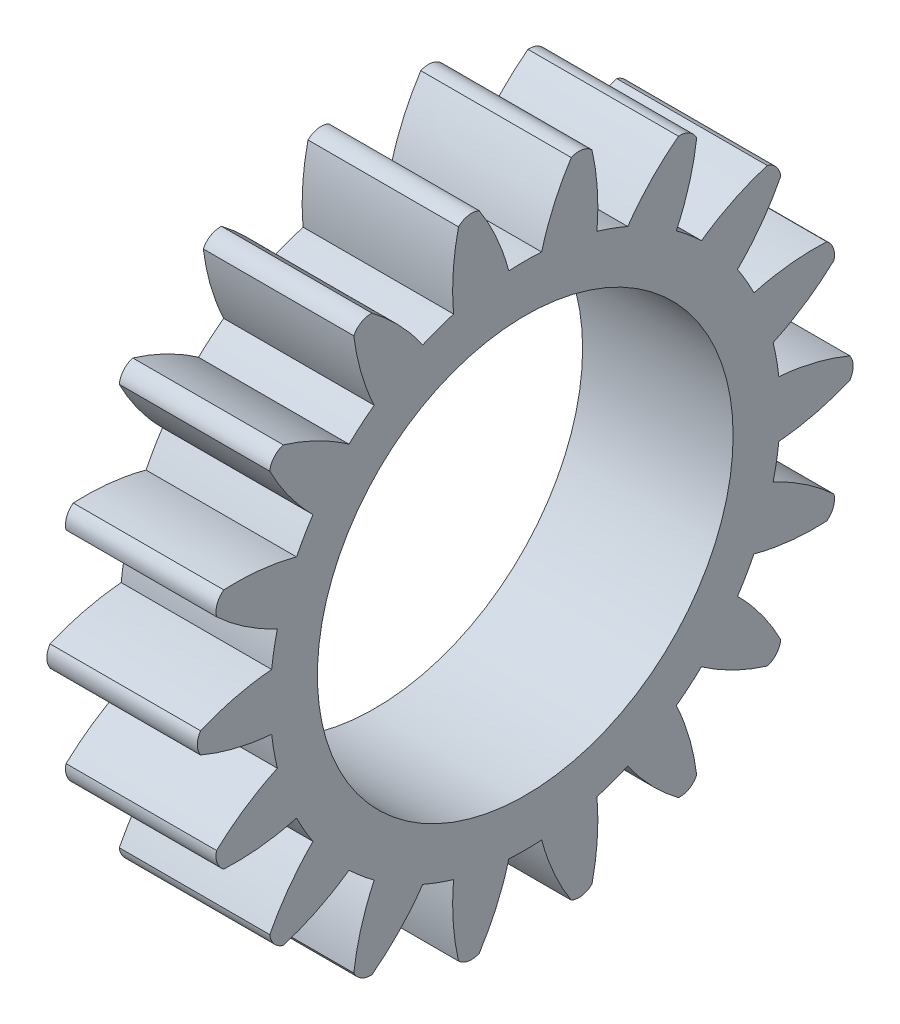
SolidWorks part; units mm, degrees
material "PLA personnalisé"
ref_plane "Plane1" through (0, 0, 0) normal (0, 0, 1) x (1, 0, 0)
ref_plane "Plane2" through (0, 0, 0) normal (0, 1, 0) x (1, 0, 0)
ref_plane "Plane3" through (0, 0, 0) normal (1, 0, 0) x (0, 0, -1)
other "Configuration Table"
sketch "HoldingSke" plane through (0, 0, 0) normal (0, 1, 0) x (1, 0, 0)
  line L0 (0, 0) -> (0.5435, -0.1766)
  line L1 (-15, 0) -> (100, 0) construction
  line L2 (0, 0) -> (-2.1039, 2.3779)
  line L3 (0, 0) -> (-11.863, 4.5341)
  line L4 (0, 0) -> (8.2133, 2.6687)
  line L5 (0, 0) -> (-46.8476, -17.4728)
  line L6 (0, 0) -> (-6.6317, -4.4744)
  line L7 (-2.1039, 2.3779) -> (8.6586, 51.2059)
  line L8 (-76.2, 54.61) -> (-74.8, 54.61)
  line L9 (-71.009, 38.7566) -> (-53.1078, 45.2721)
  line L10 (-76.2, 71.12) -> (104.1128, 71.12)
  line L11 (0, 0) -> (-8, 0)
  line L12 (-76.2, 101.6) -> (-76.147, 101.6)
  line L13 (24.9733, 27.94) -> (52.9518, 28.4284)
  line L14 (24.9733, 27.94) -> (24.9743, 27.94)
  line L15 (24.9733, 27.94) -> (100.4006, 29.5858)
  line L16 (-63.627, -1.75) -> (-12.827, -1.75)
  circle A0 centre (0, 0) radius 4
  circle A1 centre (0, 0) radius 13.5615
  circle A2 centre (0, 0) radius 37.5
  circle A3 centre (0, 0) radius 4
  dimension "MHD" = 27.123
  dimension "Hub_dia" = 75
  dimension "Bore" = 8
  dimension "MBD" = 8
  dimension "Num_teeth" = 18
  dimension "Pitch" = 0.5714
  dimension "Overall_len" = 50
  dimension "Show_teeth" = 18
  dimension "Thickness" = 8
  dimension "OAL" = 50.0001
  dimension "T_dim" = 1.4
  dimension "Ap" = 20
  dimension "H" = 19.05
  dimension "Pitch_radius" = 180.3128
  dimension "Width" = 8
  dimension "Backlash" = 0.053
  dimension "Addendum_fac" = 1
  dimension "Dedendum_fac" = 1.25
  dimension "Clearance_fac" = 0.25
  dimension "Dedendum_add" = 0.001
  dimension "Module" = 1.75
sketch "BasProSke" plane through (0, 0, 0) normal (0, 1, 0) x (1, 0, 0)
  line L0 (-10, 0) -> (60, 0) construction
  line L1 (0, 0) -> (0, 17.5)
  line L2 (0, 0) -> (8, 0)
  line L3 (8, 0) -> (8, 17.5)
  line L4 (8, 17.5) -> (0, 17.5)
  dimension "Thickness" = 8
  dimension "Diameter" = 35
revolve "Base-Revolve" add sketch "BasProSke" angle 360 about L0
sketch "TooCutSke" plane through (0, 0, 0) normal (1, 0, 0) x (0, 0, -1)
  line L1 (0, 0) -> (0, 107) construction
  line L2 (0, 0) -> (-1.4654, 15.6817) construction
  line L3 (0, 0) -> (-5.4518, 30.9188) construction
  line L4 (-1.4654, 15.6817) -> (-2.7259, 15.4594) construction
  arc A0 (0.8733, 13.5334) -> (-0.8733, 13.5334) centre (0, 0) ccw
  arc A1 (2.6093, 17.3301) -> (-2.6093, 17.3301) centre (0, 0) ccw
  circle A2 centre (0, 0) radius 15.75 construction
  circle A3 centre (0, 0) radius 14.8002 construction
  arc A4 (-0.8733, 13.5334) -> (-2.6093, 17.3301) centre (-7.1472, 12.96) ccw
  arc A5 (2.6093, 17.3301) -> (0.8733, 13.5334) centre (7.1472, 12.96) ccw
  dimension "Root_dia" = 27.123
  dimension "Overcut_dia" = 35.0508
  dimension "Pitch_dia" = 31.5
  dimension "Base_dia" = 29.6003
  dimension "Flank_rad" = 6.3
  dimension "Half_ang" = 10
  dimension "Half_CT" = 1.28
extrude "ToothCut" cut sketch "TooCutSke" along normal through all
fillet "Breaks" [suppressed] radius 0.035
fillet "RootFillets" [suppressed] radius 0.4385
pattern_circular "TeethCuts" count 18 every 20 about axis through (-10, 0, 0) along (1, 0, 0) of "ToothCut", "RootFillets", "Breaks"
sketch "HubNeaOneSke" plane through (0, 0, 0) normal (-1, 0, 0) x (0, 0, 1)
  circle A0 centre (0, 0) radius 13.5615
  dimension "Diameter" = 27.123
extrude "HubNearOne" [suppressed] add sketch "HubNeaOneSke" along normal blind 42.0001
sketch "HubNeaBotSke" plane through (0, 0, 0) normal (-1, 0, 0) x (0, 0, 1)
  circle A0 centre (0, 0) radius 13.5615
  dimension "Diameter" = 27.123
extrude "HubNearBoth" [suppressed] add sketch "HubNeaBotSke" along normal blind 21
ref_plane "FarPln" through (8, 0, 0) normal (1, 0, 0) x (0, 0, -1)
sketch "HubFarSke" plane through (8, 0, 0) normal (1, 0, 0) x (0, 0, -1)
  circle A0 centre (0, 0) radius 13.5615
  dimension "Diameter" = 27.123
extrude "HubFar" [suppressed] add sketch "HubFarSke" along normal blind 21
sketch "BorSke" plane through (0, 0, 0) normal (1, 0, 0) x (0, 0, -1)
  circle A0 centre (0, 0) radius 4
  dimension "Diameter" = 8
extrude "Bore" cut sketch "BorSke" along normal mid plane 100.0001
sketch "KeySke" plane through (0, 0, 0) normal (1, 0, 0) x (0, 0, -1)
  line L0 (-1.5, 0) -> (-1.5, 5.4)
  line L1 (-1.5, 5.4) -> (1.5, 5.4)
  line L2 (1.5, 5.4) -> (1.5, 0)
  line L3 (0, 0) -> (0, 34) construction
  line L4 (-1.5, 0) -> (1.5, 0)
  dimension "Offset" = 5.4
  dimension "Width" = 3
extrude "Keyway" [suppressed] cut sketch "KeySke" along normal mid plane 100.0001
pattern_circular "Keyway2" [suppressed] count 2 every 90 about axis through (-10, 0, 0) along (1, 0, 0)
sketch "Esquisse1" plane through (8, 0, 0) normal (1, 0, 0) x (0, 0, -1)
  circle A0 centre (0, 0) radius 11.05
  dimension "D1" = 22.1
extrude "Enlèv. mat.-Extru.1" cut sketch "Esquisse1" against normal blind 10
sketch "Esquisse3" plane through (8, 0, 0) normal (1, 0, 0) x (0, 0, -1)
  line L0 (0, 0) -> (17.5, 0) construction
  line L1 (17.494, 0.457) -> (15.5741, 1.3132) construction
  line L2 (15.5741, 1.3132) -> (13.4794, 1.49) construction
  line L3 (13.4794, 1.49) -> (13.914, 2.1775)
  line L4 (13.914, 2.1775) -> (17.9524, 1.0519)
  line L5 (17.9524, 1.0519) -> (17.494, 0.457)
  line L6 (17.9524, 1.0519) -> (17.6593, 0)
  line L7 (17.6593, 0) -> (17.5, 0)
  line L8 (17.5, 0) -> (16.43, 0)
  arc A0 (17.494, -0.457) -> (17.494, 0.457) centre (0, 0) ccw construction
  circle A2 centre (16.43, 0) radius 1
  spline S0 degree 2 poles (17.494, 0.457) (15.5741, 1.3132) (13.4794, 1.49) knots 0 0 0 1 1 1
  dimension "D1" = 2
  dimension "D2" = 1.07
extrude "Enlèv. mat.-Extru.2" cut sketch "Esquisse3" against normal blind 10 contours S0 L5 L4 L3 A2 | L5 S0 A2 L7 L6 | S0 A2
mirror "Symétrie1" about plane through (0, 0, 0) normal (0, 1, 0) of "Enlèv. mat.-Extru.2"
pattern_circular "Répétition circulaire1" count 18 over 360 about axis through (-2, 0, 0) along (1, 0, 0) of "Enlèv. mat.-Extru.2", "Symétrie1"
equation "' \"Module@HoldingSke\" = 6.35"
equation "' \"Num_teeth@HoldingSke\" = 12"
equation "' \"Ap@HoldingSke\" =  20"
equation "' \"Ap@HoldingSke\" = 20"
equation "' \"Width@HoldingSke\" = 0.5 * 25.4"
equation "' \"Hub_dia@HoldingSke\"= 1 * 25.4"
equation "' \"Hub_dia@HoldingSke\" = 1 * 25.4"
equation "' \"Overall_len@HoldingSke\" = 1.0 * 25.4"
equation "' \"Bore@HoldingSke\" = 0.75 * 25.4"
equation "' \"T_dim@HoldingSke\" = 0.1 * 25.4"
equation "' \"Width@KeySke\" = 0.25 * 25.4"
equation "' \"Show_teeth@HoldingSke\" = 13"
equation "' \"Backlash@HoldingSke\" = 0.009 * 25.4"
equation "' \"Addendum_fac@HoldingSke\" = 1.0"
equation "' \"Dedendum_fac@HoldingSke\" = 1.25"
equation "' \"Dedendum_add@HoldingSke\" = 0.00005 * 25.4"
equation "' \"Clearance_fac@HoldingSke\" = 0.25"
equation "\"Pitch@HoldingSke\" = 1 / \"Module@HoldingSke\""
equation "\"Overcut_dia@TooCutSke\" = (\"Num_teeth@HoldingSke\" + 2 * \"Addendum_fac@HoldingSke\") / \"Pitch@HoldingSke\" + 0.002 * 25.4"
equation "\"Pitch_dia@TooCutSke\" = \"Num_teeth@HoldingSke\" / \"Pitch@HoldingSke\""
equation "\"Base_dia@TooCutSke\" = \"Num_teeth@HoldingSke\" / \"Pitch@HoldingSke\" * cos((\"Ap@HoldingSke\"  * 3.14159265 / 180))"
equation "\"Root_dia@TooCutSke\" = (\"Num_teeth@HoldingSke\" + 2) / \"Pitch@HoldingSke\" - 2 * (\"Addendum_fac@HoldingSke\" + \"Dedendum_fac@HoldingSke\") / \"Pitch@HoldingSke\" - \"Dedendum_add@HoldingSke\" * 2"
equation "\"Half_ang@TooCutSke\" = 180 / \"Num_teeth@HoldingSke\""
equation "\"Half_CT@TooCutSke\" = \"Num_teeth@HoldingSke\" / \"Pitch@HoldingSke\" * sin((3.14159265 / 2 / \"Num_teeth@HoldingSke\")) / 2 - 7 * \"Backlash@HoldingSke\" / 4"
equation "\"Flank_rad@TooCutSke\" = \"Num_teeth@HoldingSke\" / \"Pitch@HoldingSke\" / 5"
equation "\"Radius@RootFillets\" = \"Clearance_fac@HoldingSke\" / \"Pitch@HoldingSke\" + \"Dedendum_add@HoldingSke\""
equation "\"Break_rad@Breaks\" = 0.02 / \"Pitch@HoldingSke\""
equation "\"Thickness@HoldingSke\" = \"Width@HoldingSke\""
equation "\"OAL@HoldingSke\" = \"Thickness@HoldingSke\""
equation "\"MHD@HoldingSke\" = (\"Num_teeth@HoldingSke\" + 2) / \"Pitch@HoldingSke\" - 2 * (\"Addendum_fac@HoldingSke\" + \"Dedendum_fac@HoldingSke\")  / \"Pitch@HoldingSke\" - \"Dedendum_add@HoldingSke\" * 2"
equation "\"MBD@HoldingSke\" = (\"Num_teeth@HoldingSke\" + 2) / \"Pitch@HoldingSke\" - 2 * (\"Addendum_fac@HoldingSke\" + \"Dedendum_fac@HoldingSke\")  / \"Pitch@HoldingSke\" - \"Dedendum_add@HoldingSke\" * 2 - 0.002 * 25.4"
equation "\"MHD@HoldingSke\" = ((sgn( \"MHD@HoldingSke\" - \"Hub_dia@HoldingSke\" )-1)*( \"MHD@HoldingSke\" - \"Hub_dia@HoldingSke\" ))/-2+ \"Hub_dia@HoldingSke\""
equation "\"MBD@HoldingSke\" = ((sgn( \"MBD@HoldingSke\" - \"Bore@HoldingSke\" )-1)*( \"MBD@HoldingSke\" - \"Bore@HoldingSke\" ))/-2+ \"Bore@HoldingSke\""
equation "\"OAL@HoldingSke\" = ((sgn( \"OAL@HoldingSke\" - \"Overall_len@HoldingSke\" )+1)*( \"OAL@HoldingSke\" - \"Overall_len@HoldingSke\" ))/2 + \"Overall_len@HoldingSke\" + 0.000002 * 25.4"
equation "\"Num_teeth@TeethCuts\" = int( \"Show_teeth@HoldingSke\" ) + 1"
equation "\"Num_teeth@TeethCuts\" = ((sgn( \"Num_teeth@TeethCuts\" - \"Num_teeth@HoldingSke\" )-1)*( \"Num_teeth@TeethCuts\" - \"Num_teeth@HoldingSke\" ))/-2+ \"Num_teeth@HoldingSke\""
equation "\"Num_teeth@TeethCuts\" = ((sgn( \"Num_teeth@TeethCuts\" - 2.0)+1)*( \"Num_teeth@TeethCuts\" - 2.0))/2 +2.0"
equation "\"Angle@TeethCuts\" = 360.0 / \"Num_teeth@HoldingSke\""
equation "\"Diameter@BasProSke\" = (\"Num_teeth@HoldingSke\" + 2 * \"Addendum_fac@HoldingSke\") / \"Pitch@HoldingSke\""
equation "\"Thickness@BasProSke\"  = \"Thickness@HoldingSke\""
equation "' \"Fillet_rad@BasProSke\" =  \"Thickness@HoldingSke\" * 0.05"
equation "' \"Fillet_rad@BasProSke\" = \"Thickness@HoldingSke\" * 0.05"
equation "\"MHD@HoldingSke\" = ((sgn( \"MHD@HoldingSke\" - \"Root_dia@TooCutSke\" )-1)*( \"MHD@HoldingSke\" - \"Root_dia@TooCutSke\" ))/-2+ \"Root_dia@TooCutSke\""
equation "\"Diameter@HubNeaOneSke\" = \"MHD@HoldingSke\""
equation "\"Length@HubNearOne\" = \"OAL@HoldingSke\" - \"Thickness@BasProSke\""
equation "\"Diameter@HubNeaBotSke\" = \"MHD@HoldingSke\""
equation "\"Length@HubNearBoth\" = ( \"OAL@HoldingSke\" - \"Thickness@BasProSke\" ) / 2.0"
equation "\"Thickness@FarPln\" = \"Thickness@BasProSke\""
equation "\"Diameter@HubFarSke\" = \"MHD@HoldingSke\""
equation "\"Length@HubFar\" = ( \"OAL@HoldingSke\" - \"Thickness@BasProSke\" ) / 2.0"
equation "\"Diameter@BorSke\" = \"MBD@HoldingSke\""
equation "\"D1@Bore\" = \"OAL@HoldingSke\" * 2.0"
equation "\"D1@Keyway\" = \"OAL@HoldingSke\" * 2.0"
equation "\"Offset@KeySke\" = \"T_dim@HoldingSke\" + \"MBD@HoldingSke\" / 2.0"
